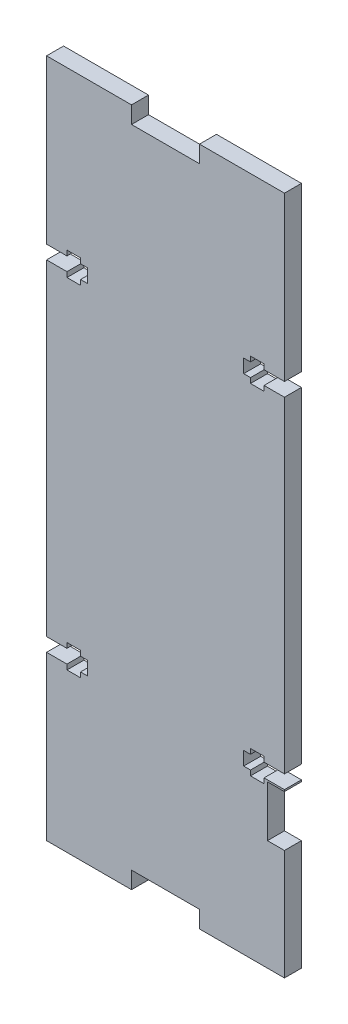
SolidWorks part; units mm, degrees
ref_plane "Front Plane" through (0, 0, 0) normal (0, 0, 1) x (1, 0, 0)
ref_plane "Top Plane" through (0, 0, 0) normal (0, 1, 0) x (1, 0, 0)
ref_plane "Right Plane" through (0, 0, 0) normal (1, 0, 0) x (0, 0, -1)
sketch "Sketch2" plane through (0, 0, 0) normal (0, 0, 1) x (1, 0, 0)
  line L0 (0, 100) -> (0, -100) construction
  line L1 (-35, 100) -> (35, 100)
  line L2 (-35, 100) -> (-35, -100)
  line L3 (-35, -100) -> (-10, -100)
  line L4 (35, 100) -> (35, -100)
  line L5 (-35, 100) -> (35, -100) construction
  line L6 (-35, -100) -> (35, 100) construction
  line L7 (-35, 0) -> (35, 0) construction
  line L8 (-10, 100) -> (-10, 95)
  line L9 (10, 100) -> (10, 95)
  line L12 (10, -100) -> (35, -100)
  line L14 (-10, -95) -> (10, -95)
  line L16 (10, -95) -> (10, -100)
  line L17 (-10, -95) -> (-10, -100)
  line L18 (10, 100) -> (10, -100) construction
  line L19 (-10, 95) -> (10, 95)
  line L20 (-10, 100) -> (-10, -100) construction
  point P0 (0, 0)
  point P14 (-25, -65)
  point P15 (25, -65)
  point P16 (-25, 65)
  point P17 (25, 65)
  dimension "D1" = 200
  dimension "D2" = 70
  dimension "D3" = 10
  dimension "D4" = 10
  dimension "D5" = 5
  dimension "D7" = 20
extrude "Boss-Extrude1" add sketch "Sketch2" along normal blind 5 contours L19 L8 L1 L2 L3 L17 L14 L16 L12 L4 L9
sketch "Sketch3" plane through (0, 0, 5) normal (0, 0, 1) x (1, 0, 0)
  line L0 (-34.6023, 0) -> (32.5846, 0) construction
  line L1 (-35, 100) -> (-35, -100) construction
  line L2 (35, 100) -> (35, -100) construction
  line L3 (-39.2646, -50) -> (23.2996, -50) construction
  line L4 (35, -52) -> (29, -52)
  line L5 (29, -52) -> (29, -53.5)
  line L6 (29, -53.5) -> (25, -53.5)
  line L7 (25, -53.5) -> (25, -52)
  line L8 (25, -52) -> (23, -52)
  line L9 (23, -52) -> (23, -48)
  line L10 (23, -48) -> (25, -48)
  line L11 (25, -48) -> (25, -46.5)
  line L12 (25, -46.5) -> (29, -46.5)
  line L13 (29, -46.5) -> (29, -48)
  line L14 (29, -48) -> (35, -48)
  line L15 (35, -48) -> (35, -52)
  line L16 (-35, -100) -> (-10, -100) construction
  dimension "D1" = 50
  dimension "D2" = 4
  dimension "D3" = 0
  dimension "D4" = 25
  dimension "D5" = 12
  dimension "D6" = 2
  dimension "D7" = 3.5
  dimension "D8" = 2
  dimension "D10" = 200
extrude "Cut-Extrude1" cut sketch "Sketch3" against normal blind 10
mirror "Mirror1" about plane through (0, 0, 0) normal (0, 1, 0) of "Cut-Extrude1"
mirror "Mirror2" about plane through (0, 0, 0) normal (1, 0, 0) of "Mirror1", "Cut-Extrude1"
sketch "Sketch4" plane through (0, 0, 0) normal (0, 0, -1) x (-1, 0, 0)
  line L1 (-35, -52.5) -> (-30, -52.5)
  line L2 (-35, -52.5) -> (-35, -67.5)
  line L3 (-35, -67.5) -> (-30, -67.5)
  line L4 (-30, -52.5) -> (-30, -67.5)
  line L5 (-35, -52.5) -> (-30, -67.5) construction
  line L6 (-35, -67.5) -> (-30, -52.5) construction
  line L8 (35, -100) -> (10, -100) construction
  line L10 (-35, 48) -> (-35, -48) construction
  point P0 (-32.5, -60)
  dimension "D1" = 15
  dimension "D2" = 5
  dimension "D3" = 2.5
  dimension "D4" = 40
extrude "Cut-Extrude2" cut sketch "Sketch4" against normal blind 10
